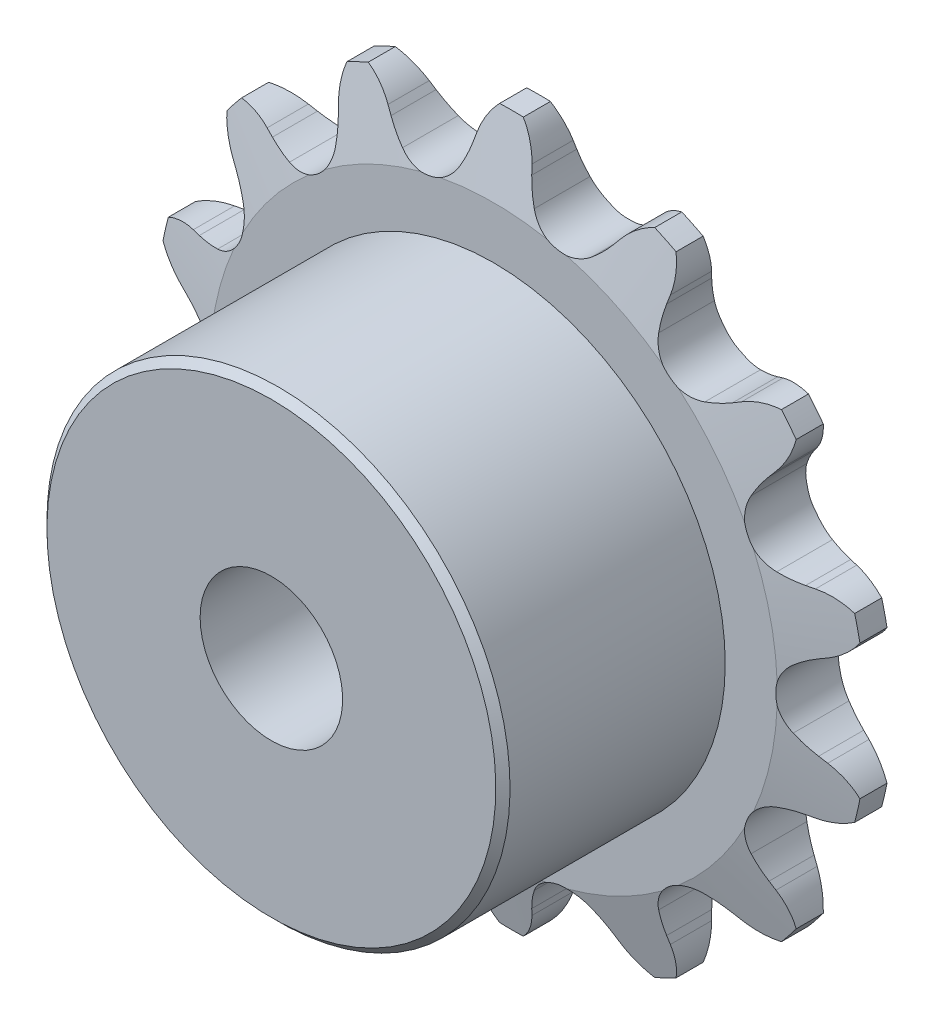
SolidWorks part; units mm, degrees
ref_plane "Front Plane" through (0, 0, 0) normal (0, 0, 1) x (1, 0, 0)
ref_plane "Top Plane" through (0, 0, 0) normal (0, 1, 0) x (1, 0, 0)
ref_plane "Right Plane" through (0, 0, 0) normal (1, 0, 0) x (0, 0, -1)
sketch "Sketch0" plane through (0, 0, 0) normal (0, 0, 1) x (1, 0, 0)
  line L0 (3.175, -13.9106) -> (0, 0) construction
  line L1 (0, 0) -> (8.8962, -11.1554) construction
  line L2 (0, 0) -> (-3.175, -13.9106) construction
  line L3 (3.175, -13.9106) -> (8.8962, -11.1554) construction
  line L4 (3.175, -13.9106) -> (-3.175, -13.9106) construction
  line L5 (5.1861, -13.5963) -> (4.9663, -13.3164)
  line L6 (3.175, -13.9106) -> (0, -14.6353) construction
  line L7 (1.2267, -14.5) -> (1.3033, -14.1525)
  line L8 (0, -13.9106) -> (0, -15.8156) construction
  line L9 (4.2167, -12.5704) -> (1.5539, -15.9962) construction
  line L10 (0, 0) -> (0, -13.9106) construction
  line L11 (4.9663, -13.3164) -> (1.5539, -15.9962) construction
  line L12 (0, -15.8156) -> (0, -16.2352) construction
  line L13 (7.34, -11.9048) -> (5.1861, -13.5963) construction
  circle A0 centre (0, 0) radius 15.8156 construction
  circle A1 centre (0, 0) radius 14.2683 construction
  arc A2 (-1.7313, -16.6345) -> (8.7773, -14.236) centre (0, 0) ccw
  circle A3 centre (0, 0) radius 16.2352 construction
  circle A4 centre (3.175, -13.9106) radius 1.651 construction
  arc A7 (4.2167, -12.5704) -> (1.655, -13.1551) centre (3.175, -13.9106) ccw
  circle A8 centre (3.175, -13.9106) radius 1.6974 construction
  arc A9 (5.1861, -13.5963) -> (8.7773, -14.236) centre (7.34, -11.9048) ccw
  arc A10 (4.9663, -13.3164) -> (4.2167, -12.5704) centre (1.5539, -15.9962) ccw
  arc A11 (1.2267, -14.5) -> (-1.7313, -16.6345) centre (-1.4478, -13.9106) cw
  arc A12 (1.3033, -14.1525) -> (1.655, -13.1551) centre (5.5405, -15.0863) cw
  dimension "D1" = 1.6974
  dimension "R" = 1.6974
sketch "Sketch1" plane through (0, 0, 0) normal (1, 0, 0) x (0, 0, -1)
  line L0 (1.397, 0) -> (-1.397, 0)
  line L1 (-1.397, 0) -> (-1.397, 12.6406)
  line L2 (-1.397, 12.6406) -> (-0.6033, 15.8156)
  line L3 (-0.6033, 15.8156) -> (0.6033, 15.8156)
  line L4 (0.6033, 15.8156) -> (1.397, 12.6406)
  line L5 (1.397, 12.6406) -> (1.397, 0)
  line L7 (0, 15.8156) -> (0, 0) construction
  line L8 (-1.397, 12.6406) -> (1.397, 12.6406) construction
  line L9 (0, 15.8156) -> (0, -15.8156) construction
  line L10 (-1.397, 12.6406) -> (-1.397, 15.8156) construction
  line L11 (-1.397, 15.8156) -> (-0.6033, 15.8156) construction
  line L12 (0.6033, 15.8156) -> (1.397, 15.8156) construction
  line L13 (1.397, 15.8156) -> (1.397, 12.6406) construction
  line L14 (0, 0) -> (-6.4008, 0) construction
  line L22 (1.397, 0) -> (-11.303, 0) construction
  line L24 (-1.397, 0) -> (-1.397, 10.3546) construction
revolve "Revolve1" add sketch "Sketch1" angle 360 mid plane about L0
extrude "Cut-Extrude1" cut sketch "Sketch0" against normal through all and the other way through all
pattern_circular "CirPattern1" count 14 over 360 about axis through (0, 0, 0) along (0, 0, 1) of "Cut-Extrude1"
sketch "Sketch2" plane through (0, 0, 0) normal (0, 0, 1) x (1, 0, 0)
  circle A0 centre (0, 0) radius 3.175 construction
  circle A1 centre (0, 0) radius 10.3188
  circle A2 centre (0, 0) radius 15.875 construction
  dimension "Bore" = 6.35
  dimension "Hub Dia." = 20.6375
  dimension "OD" = 31.75
extrude "Boss-Extrude1" add sketch "Sketch2" along normal up to vertex (11.303 mm away) from surface at 1.397 starting at face at (0, 0, 1.397)
sketch "Sketch3" plane through (0, 0, 0) normal (0, 0, 1) x (1, 0, 0)
  circle A0 centre (0, 0) radius 3.175 construction
  circle A1 centre (0, 0) radius 3.175
extrude "Cut-Extrude2" cut sketch "Sketch3" along normal through all and the other way through all
sketch "Sketch4" plane through (0, 0, 0) normal (1, 0, 0) x (0, 0, -1)
  line L0 (-11.303, 10.3188) -> (-11.303, 10.0013)
  line L1 (-1.397, 15.8156) -> (-3.4925, 15.8156)
  line L2 (-1.397, 15.8156) -> (-1.397, 10.3546)
  line L3 (-1.397, 10.3546) -> (-3.4925, 10.3546)
  line L4 (-3.4925, 15.8156) -> (-3.4925, 10.3546)
  line L9 (-11.303, 10.0013) -> (-10.9855, 10.3188)
  line L10 (-10.9855, 10.3188) -> (-11.303, 10.3188)
  dimension "C" = 0.3175
  dimension "D3" = 2.0955
revolve "Cut-Revolve1" cut sketch "Sketch4" angle 360 mid plane about L22
equation "\"360/N@Sketch0\" = 360/\"Teeth@CirPattern1\""
equation "\"Ds@Sketch0\" = 1.005 * \"Dr@Sketch0\" + 0.003"
equation "\"R@Sketch0\" = 1/2 * \"Ds@Sketch0\""
equation "\"A@Sketch0\" = 35 +  ( 60 / \"Teeth@CirPattern1\" ) "
equation "\"B@Sketch0\" = 18 -  ( 56 / \"Teeth@CirPattern1\" )"
equation "\"ac@Sketch0\" = 0.8 * \"Dr@Sketch0\""
equation "\"ab@Sketch0\" = 1.4 * \"Dr@Sketch0\""
equation "\"J@Sketch0\" = 0.3 * \"Pitch@Sketch0\""
equation "\"h@Sketch1\" = \"Pitch@Sketch0\" / 2"
equation "\"g@Sketch1\" = \"h@Sketch1\" / 4"
equation "\"MHD@Sketch1\" = \"Pitch@Sketch0\" * ( cotan ( 180 / \"Teeth@CirPattern1\" ) - 1 ) - 0.030"
equation "\"D3@Sketch4\" = \"t@Sketch1\" * 3 / 4"
